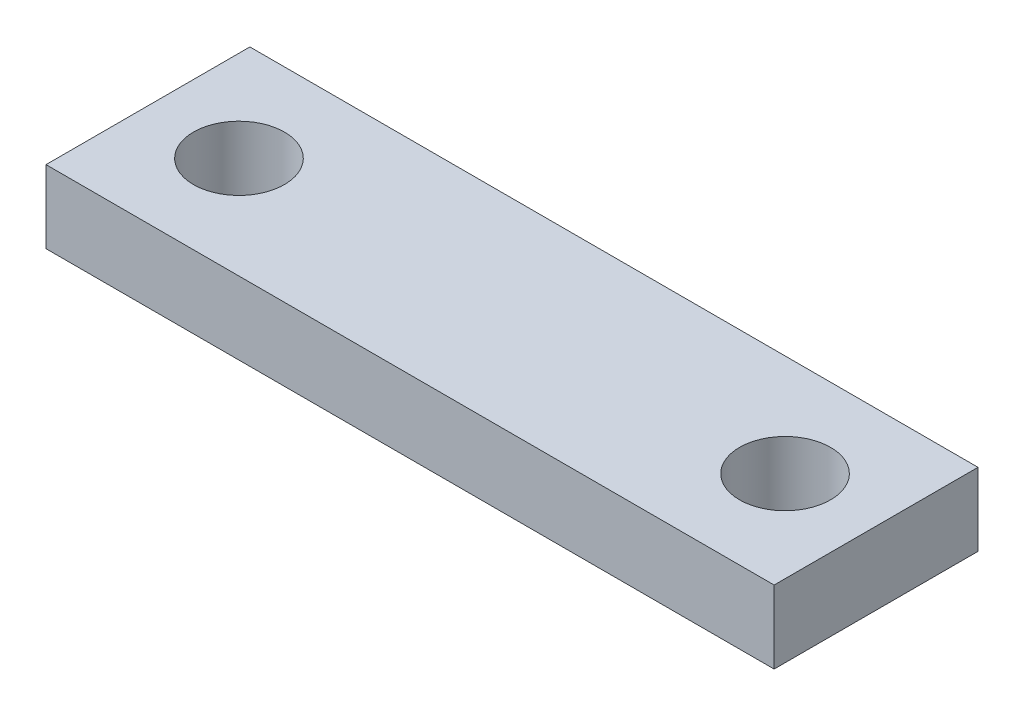
SolidWorks part; units mm, degrees
ref_plane "Front Plane" through (0, 0, 0) normal (0, 0, 1) x (1, 0, 0)
ref_plane "Top Plane" through (0, 0, 0) normal (0, 1, 0) x (1, 0, 0)
ref_plane "Right Plane" through (0, 0, 0) normal (1, 0, 0) x (0, 0, -1)
sketch "Sketch1" plane through (0, 0, 0) normal (0, 1, 0) x (1, 0, 0)
  line L0 (-15, 0) -> (15, 0) construction
  line L2 (-20, -5.6) -> (20, -5.6)
  line L3 (-20, -5.6) -> (-20, 5.6)
  line L4 (-20, 5.6) -> (20, 5.6)
  line L5 (20, -5.6) -> (20, 5.6)
  line L6 (-20, -5.6) -> (20, 5.6) construction
  line L7 (-20, 5.6) -> (20, -5.6) construction
  circle A0 centre (-15, 0) radius 2.5
  circle A1 centre (15, 0) radius 2.5
  point P4 (0, 0)
  point P10 (-465.2895, 142.24)
  point P11 (404.0387, -168.3464)
  point P12 (0, 0)
  dimension "D1" = 5
  dimension "D2" = 11.2
  dimension "D3" = 30
  dimension "D4" = 40
extrude "Boss-Extrude2" add sketch "Sketch1" along normal blind 4
